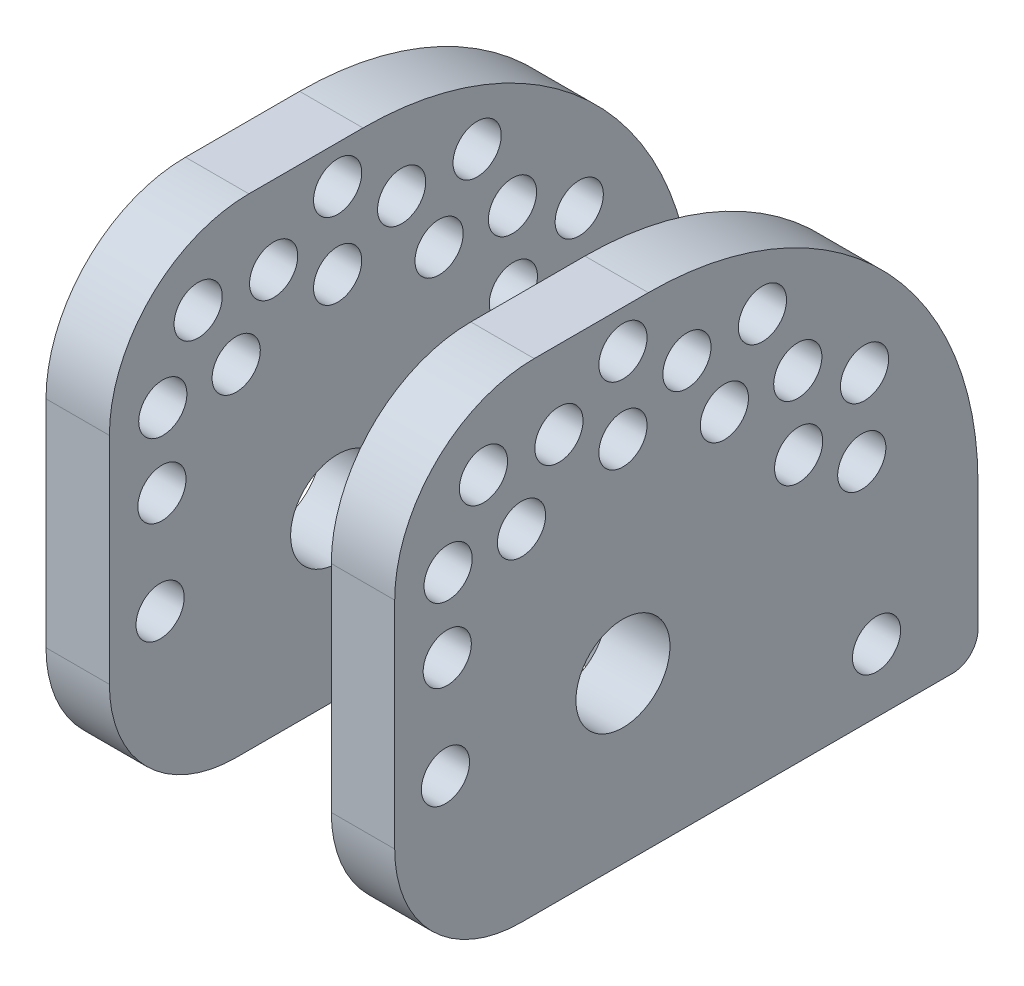
SolidWorks part; units mm, degrees
material "6061-T6 (SS)"
ref_plane "Front Plane" through (0, 0, 0) normal (0, 0, 1) x (1, 0, 0)
ref_plane "Top Plane" through (0, 0, 0) normal (0, 1, 0) x (1, 0, 0)
ref_plane "Right Plane" through (0, 0, 0) normal (1, 0, 0) x (0, 0, -1)
sketch "Top Outline" plane through (0, 0, 0) normal (0, 1, 0) x (1, 0, 0)
  line L0 (-133.35, -22.86) -> (133.35, -22.86) construction
  line L1 (-82.55, 0) -> (82.55, 0) construction
  line L2 (-58.42, 156.21) -> (-58.42, 0) construction
  line L3 (-58.42, 156.21) -> (58.42, 156.21) construction
  line L4 (58.42, 156.21) -> (58.42, 0) construction
  line L5 (0, 156.21) -> (0, 0) construction
  line L6 (-33.02, 156.21) -> (-33.02, 0) construction
  line L7 (33.02, 156.21) -> (33.02, 0) construction
  line L8 (-82.55, 56.515) -> (82.55, 56.515) construction
  line L9 (-58.42, 147.32) -> (58.42, 147.32) construction
  line L10 (0, 0) -> (0, -22.86) construction
  line L11 (-58.42, 73.66) -> (58.42, 73.66) construction
  line L12 (-133.35, -22.86) -> (-133.35, 156.21) construction
  line L13 (133.35, -22.86) -> (133.35, 156.21) construction
  circle A0 centre (-82.55, 0) radius 3.175 construction
  circle A1 centre (-82.55, 56.515) radius 3.175 construction
  circle A2 centre (82.55, 56.515) radius 3.175 construction
  circle A3 centre (82.55, 0) radius 3.175 construction
  point P7 (0, 56.515)
  point P8 (0, -22.86)
  point P21 (0, 0)
  dimension "D11" = 6.35
  dimension "D1" = 156.21
  dimension "D2" = 22.86
  dimension "D3" = 66.04
  dimension "D4" = 33.02
  dimension "D5" = 25.4
  dimension "D6" = 56.515
  dimension "D7" = 8.89
  dimension "D8" = 266.7
  dimension "D9" = 73.66
  dimension "D10" = 165.1
sketch "Side Outline" plane through (0, 0, 0) normal (1, 0, 0) x (0, 0, -1)
  line L0 (0, 0) -> (156.21, 0) construction
  line L1 (-22.86, 0) -> (156.21, 0) construction
  line L2 (0, 0) -> (0, 25.4) construction
  line L3 (156.21, 15.24) -> (0, 15.24) construction
  line L4 (0, 25.4) -> (156.21, 25.4) construction
  line L5 (156.21, 25.4) -> (156.21, 0) construction
  line L6 (-22.86, 74.6333) -> (-22.86, 0) construction
  line L7 (-22.86, 0) -> (0, 0) construction
  line L8 (-22.86, 74.6333) -> (147.32, 16.51) construction
  line L9 (73.66, 15.24) -> (73.66, 0) construction
  line L10 (56.515, 0) -> (56.515, 15.24) construction
  circle A0 centre (147.32, 16.51) radius 3.9624 construction
  circle A1 centre (-22.86, 16.51) radius 3.175 construction
  dimension "D5" = 7.9248
  dimension "D10" = 6.35
  dimension "D1" = 156.21
  dimension "D2" = 22.86
  dimension "D3" = 25.4
  dimension "D4" = 16.51
  dimension "D6" = 73.66
  dimension "D7" = 15.24
  dimension "D8" = 8.89
  dimension "D9" = 16.51
  dimension "D11" = 179.832
  dimension "D12" = 56.515
sketch "Sketch1" plane through (0, 0, 0) normal (1, 0, 0) x (0, 0, -1)
  line L0 (-12.7, 0) -> (-12.7, 15.24)
  line L1 (-22.86, 0) -> (156.21, 0) construction
  line L2 (-12.7, 15.24) -> (138.43, 15.24)
  line L3 (156.21, 15.24) -> (0, 15.24) construction
  line L4 (138.43, 15.24) -> (138.43, 16.51)
  line L5 (156.21, 0) -> (156.21, 16.51)
  line L6 (156.21, 25.4) -> (156.21, 0) construction
  line L8 (156.21, 0) -> (-12.7, 0)
  line L9 (0, 0) -> (0, 25.4) construction
  arc A0 (138.43, 16.51) -> (156.21, 16.51) centre (147.32, 16.51) cw
  dimension "D4" = 8.89
  dimension "D1" = 15.24
  dimension "D2" = 12.7
  dimension "D3" = 168.91
extrude "Center MC Body " add sketch "Sketch1" along normal blind 9.525
sketch "Sketch2" plane through (0, 0, 0) normal (1, 0, 0) x (0, 0, -1)
  line L0 (156.21, 25.4) -> (156.21, 0) construction
  line L1 (-22.86, 0) -> (156.21, 0) construction
  circle A0 centre (147.32, 16.51) radius 3.9624
  dimension "D3" = 7.9248
  dimension "D1" = 8.89
  dimension "D2" = 16.51
extrude "Center MC Hole" cut sketch "Sketch2" along normal blind 9.525
sketch "Sketch3" plane through (0, 0, 0) normal (1, 0, 0) x (0, 0, -1)
  line L0 (-6.35, 15.24) -> (12.7, 15.24)
  line L1 (156.21, 15.24) -> (0, 15.24) construction
  line L2 (12.7, 15.24) -> (12.7, 8.89)
  line L3 (12.7, 8.89) -> (-6.35, 8.89)
  line L5 (-6.35, 8.89) -> (-6.35, 15.24)
  line L6 (43.815, 15.24) -> (69.215, 15.24)
  line L7 (69.215, 15.24) -> (69.215, 8.89)
  line L8 (69.215, 8.89) -> (43.815, 8.89)
  line L9 (43.815, 8.89) -> (43.815, 15.24)
  line L12 (56.515, 8.89) -> (56.515, 0) construction
  line L13 (-22.86, 0) -> (156.21, 0) construction
  dimension "D1" = 19.05
  dimension "D2" = 25.4
  dimension "D3" = 8.89
  dimension "D4" = 56.515
  dimension "D5" = 12.7
extrude "Cut Slot" cut sketch "Sketch3" along normal blind 9.525
fillet "Fillet1" radius 12.7 1 edges at (4.7625, 0, -156.21)
fillet "Fillet2" radius 12.7 1 edges at (4.7625, 15.24, -138.43)
sketch "Sketch5" [suppressed] plane through (0, 0, 0) normal (1, 0, 0) x (0, 0, -1)
  line L0 (-12.7, 15.24) -> (43.815, 15.24)
  line L1 (43.815, 15.24) -> (43.815, 0) construction
  line L2 (156.21, 0) -> (0, 0) construction
  line L3 (43.815, 0) -> (-12.7, 0)
  line L4 (-12.7, 0) -> (-12.7, 15.24)
  arc A0 (43.815, 15.24) -> (43.815, 0) centre (43.815, 7.62) ccw
extrude "Cut-Extrude1" [suppressed] cut sketch "Sketch5" along normal through all
sketch "Sketch55" [suppressed] plane through (9.525, 0, 0) normal (1, 0, 0) x (0, 0, -1)
  line L6 (43.815, 0) -> (143.51, 0)
  line L7 (156.21, 12.7) -> (156.21, 16.51)
  line L8 (129.0038, 15.24) -> (69.215, 15.24)
  line L9 (69.215, 15.24) -> (69.215, 8.89)
  line L10 (69.215, 8.89) -> (43.815, 8.89)
  line L11 (43.815, 8.89) -> (43.815, 15.24)
  line L12 (43.815, 0) -> (143.51, 0)
  line L13 (156.21, 12.7) -> (156.21, 16.51)
  line L14 (129.0038, 15.24) -> (69.215, 15.24)
  line L15 (69.215, 15.24) -> (69.215, 8.89)
  line L16 (69.215, 8.89) -> (43.815, 8.89)
  line L17 (43.815, 8.89) -> (43.815, 15.24)
  circle A0 centre (147.32, 16.51) radius 3.9624 construction
  circle A1 centre (147.32, 16.51) radius 3.9624
  arc A4 (43.815, 15.24) -> (43.815, 0) centre (43.815, 7.62) ccw
  arc A5 (143.51, 0) -> (156.21, 12.7) centre (143.51, 12.7) ccw
  arc A6 (156.21, 16.51) -> (139.778, 21.2165) centre (147.32, 16.51) ccw
  arc A7 (129.0038, 15.24) -> (139.778, 21.2165) centre (129.0038, 27.94) ccw
  arc A8 (43.815, 15.24) -> (43.815, 0) centre (43.815, 7.62) ccw
  arc A9 (143.51, 0) -> (156.21, 12.7) centre (143.51, 12.7) ccw
  arc A10 (156.21, 16.51) -> (139.778, 21.2165) centre (147.32, 16.51) ccw
  arc A11 (129.0038, 15.24) -> (139.778, 21.2165) centre (129.0038, 27.94) ccw
  dimension "D1" = 0
extrude "Add Thickness 0.25" [suppressed] add sketch "Sketch55" along normal blind 6.35
sketch "Sketch56" [suppressed] plane through (0, 0, 0) normal (0, 1, 0) x (-1, 0, 0)
  line L0 (-7.9375, -129.54) -> (-7.9375, -78.74) construction
  line L1 (-12.7, -129.54) -> (-12.7, -78.74)
  line L2 (-3.175, -129.54) -> (-3.175, -78.74)
  line L3 (-7.9375, -129.0038) -> (-7.9375, -69.215) construction
  line L4 (-15.875, -129.0038) -> (0, -129.0038) construction
  line L5 (-15.875, -69.215) -> (0, -69.215) construction
  arc A0 (-12.7, -129.54) -> (-3.175, -129.54) centre (-7.9375, -129.54) ccw
  arc A1 (-3.175, -78.74) -> (-12.7, -78.74) centre (-7.9375, -78.74) ccw
  point P2 (-7.9375, -104.14)
  dimension "D1" = 9.525
  dimension "D2" = 9.525
  dimension "D3" = 50.8
extrude "Cut MC Slot" [suppressed] cut sketch "Sketch56" along normal through all
sketch "Sketch6" [suppressed] plane through (0, 0, 0) normal (0, 1, 0) x (1, 0, 0)
  line L0 (-88.9, 69.215) -> (88.9, 69.215)
  line L1 (88.9, 69.215) -> (88.9, 43.815)
  line L2 (88.9, 43.815) -> (-88.9, 43.815)
  line L3 (-88.9, 43.815) -> (-88.9, 69.215)
  line L4 (-82.55, 56.515) -> (82.55, 56.515) construction
  point P7 (0, 43.815)
  dimension "D1" = 25.4
  dimension "D2" = 12.7
  dimension "D3" = 177.8
extrude "Top Center Body" [suppressed] add sketch "Sketch6" along normal blind 15.875
sketch "Sketch7" [suppressed] plane through (0, 0, 0) normal (0, 1, 0) x (1, 0, 0)
  line L0 (-46.99, 69.215) -> (-46.99, 62.865)
  line L1 (88.9, 69.215) -> (-88.9, 69.215) construction
  line L2 (-46.99, 62.865) -> (-12.7, 62.865)
  line L3 (-12.7, 62.865) -> (-12.7, 69.215)
  line L4 (-12.7, 69.215) -> (-46.99, 69.215)
  line L5 (88.9, 43.815) -> (69.85, 43.815)
  line L6 (88.9, 50.165) -> (88.9, 43.815)
  line L7 (88.9, 50.165) -> (69.85, 50.165)
  line L8 (69.85, 50.165) -> (69.85, 43.815)
  line L9 (-88.9, 56.515) -> (88.9, 56.515) construction
  line L10 (46.99, 43.815) -> (46.99, 50.165)
  line L11 (-88.9, 69.215) -> (-88.9, 43.815) construction
  line L12 (88.9, 43.815) -> (88.9, 69.215) construction
  line L13 (0, 69.215) -> (0, 56.515) construction
  line L14 (0, 156.21) -> (0, 0) construction
  line L16 (12.7, 43.815) -> (46.99, 43.815)
  line L17 (12.7, 50.165) -> (12.7, 43.815)
  line L18 (46.99, 50.165) -> (12.7, 50.165)
  line L19 (46.99, 62.865) -> (12.7, 62.865)
  line L20 (-12.7, 50.165) -> (-12.7, 43.815)
  line L21 (-46.99, 50.165) -> (-12.7, 50.165)
  line L22 (-12.7, 43.815) -> (-46.99, 43.815)
  line L23 (-46.99, 43.815) -> (-46.99, 50.165)
  line L25 (-88.9, 62.865) -> (-69.85, 62.865)
  line L26 (-88.9, 62.865) -> (-88.9, 69.215)
  line L27 (-88.9, 69.215) -> (-69.85, 69.215)
  line L28 (-69.85, 62.865) -> (-69.85, 69.215)
  line L29 (12.7, 62.865) -> (12.7, 69.215)
  line L30 (12.7, 69.215) -> (46.99, 69.215)
  line L31 (46.99, 69.215) -> (46.99, 62.865)
  line L32 (88.9, 62.865) -> (69.85, 62.865)
  line L33 (69.85, 62.865) -> (69.85, 69.215)
  line L34 (88.9, 69.215) -> (69.85, 69.215)
  line L35 (88.9, 62.865) -> (88.9, 69.215)
  line L36 (-88.9, 50.165) -> (-69.85, 50.165)
  line L37 (-69.85, 50.165) -> (-69.85, 43.815)
  line L38 (-88.9, 43.815) -> (-69.85, 43.815)
  line L39 (-88.9, 50.165) -> (-88.9, 43.815)
  line L40 (-69.85, 69.215) -> (-46.99, 69.215) construction
  line L42 (88.9, 69.215) -> (-88.9, 69.215) construction
  point P20 (-58.42, 69.215)
  dimension "D1" = 19.05
  dimension "D2" = 58.42
  dimension "D3" = 6.35
  dimension "D4" = 12.7
extrude "Cut-Extrude31" [suppressed] cut sketch "Sketch7" along normal through all
sketch "Sketch9" [suppressed] plane through (0, 0, 0) normal (0, 1, 0) x (1, 0, 0)
  circle A0 centre (-82.55, 56.515) radius 3.175
  circle A1 centre (82.55, 56.515) radius 3.175
  dimension "D1" = 6.35
extrude "TC-Cut Holes" [suppressed] cut sketch "Sketch9" along normal through all
sketch "Sketch11" [suppressed] plane through (0, 0, -43.815) normal (0, 0, 1) x (1, 0, 0)
  line L0 (0, 0) -> (0, 8.89) construction
  line L2 (7.9375, 0) -> (-7.9375, 0)
  line L4 (-7.9375, 0) -> (-7.9375, 8.89)
  line L5 (-7.9375, 8.89) -> (7.9375, 8.89)
  line L7 (-63.1825, 0) -> (-53.6575, 0)
  line L8 (-63.1825, 0) -> (-63.1825, 8.89)
  line L9 (-63.1825, 8.89) -> (-53.6575, 8.89)
  line L10 (-53.6575, 0) -> (-53.6575, 8.89)
  line L11 (-58.42, 15.875) -> (-58.42, 0) construction
  line L13 (7.9375, 0) -> (7.9375, 8.89)
  line L14 (63.1825, 0) -> (63.1825, 8.89)
  line L15 (63.1825, 0) -> (53.6575, 0)
  line L16 (53.6575, 0) -> (53.6575, 8.89)
  line L17 (63.1825, 8.89) -> (53.6575, 8.89)
  line L18 (-20.6375, 8.89) -> (-20.6375, 0) construction
  line L19 (-25.4, 0) -> (-15.875, 0)
  line L20 (-25.4, 0) -> (-25.4, 8.89)
  line L21 (-25.4, 8.89) -> (-15.875, 8.89)
  line L22 (-15.875, 0) -> (-15.875, 8.89)
  line L23 (25.4, 0) -> (15.875, 0)
  line L24 (25.4, 0) -> (25.4, 8.89)
  line L25 (15.875, 0) -> (15.875, 8.89)
  line L26 (25.4, 8.89) -> (15.875, 8.89)
  line L28 (-69.85, 0) -> (-46.99, 0) construction
  line L29 (-12.7, 0) -> (12.7, 0) construction
  point P16 (-58.42, 0)
  point P23 (0, 8.89)
  dimension "D1" = 9.525
  dimension "D2" = 8.89
  dimension "D3" = 7.9375
  dimension "D4" = 58.42
  dimension "D5" = 15.875
  dimension "D6" = 9.525
extrude "TC-Cut Slots" [suppressed] cut sketch "Sketch11" against normal through all
fillet "Fillet8" [suppressed] radius 6.35
fillet "Fillet9" [suppressed] radius 3.175
sketch "Sketch12" plane through (0, 0, 0) normal (1, 0, 0) x (0, 0, -1)
  line L1 (56.515, 0) -> (156.21, 0)
  line L2 (56.515, 0) -> (56.515, 25.4)
  line L3 (56.515, 25.4) -> (156.21, 25.4)
  line L4 (156.21, 0) -> (156.21, 25.4)
extrude "Cut-Extrude2" cut sketch "Sketch12" along normal through all
sketch "Sketch13" plane through (0, 0, 0) normal (1, 0, 0) x (0, 0, -1)
  line L0 (43.815, 15.24) -> (50.165, 15.24)
  line L1 (50.165, 15.24) -> (50.165, 8.89)
  line L3 (50.165, 8.89) -> (62.865, 8.89)
  line L4 (62.865, 8.89) -> (62.865, 15.24)
  line L5 (62.865, 15.24) -> (66.675, 15.24)
  line L6 (66.675, 15.24) -> (66.675, 0)
  line L7 (156.21, 0) -> (0, 0) construction
  line L8 (66.675, 0) -> (43.815, 0)
  line L9 (43.815, 0) -> (43.815, 15.24)
  line L11 (56.515, 0) -> (56.515, 15.24) construction
  dimension "D1" = 6.35
  dimension "D2" = 12.7
  dimension "D3" = 3.81
extrude "Boss-Extrude1" add sketch "Sketch13" along normal up to surface (9.525 mm away) up to face at (9.525, 9.652, -18.796)
fillet "Fillet3" radius 3.175 2 edges at (4.7625, 0, -66.675) (4.7625, 15.24, -66.675)
sketch "Sketch14" plane through (0, 0, 0) normal (1, 0, 0) x (0, 0, -1)
  line L0 (-12.7, 0) -> (-35.56, 0)
  line L1 (-35.56, 0) -> (-35.56, 27.94)
  line L2 (-35.56, 27.94) -> (-12.7, 27.94)
  line L3 (-12.7, 27.94) -> (-12.7, 0)
  circle A0 centre (-22.86, 16.51) radius 4.7117
  dimension "D3" = 9.4234
  dimension "D1" = 27.94
  dimension "D2" = 22.86
extrude "Boss-Extrude2" add sketch "Sketch14" along normal blind 9.525
sketch "Sketch15" plane through (0, 0, 0) normal (1, 0, 0) x (0, 0, -1)
  line L0 (-12.7, 15.24) -> (-12.7, 27.94) construction
  line L1 (-6.35, 15.24) -> (-12.7, 15.24)
  line L2 (-6.35, 15.24) -> (-6.35, 8.89)
  line L3 (-6.35, 8.89) -> (-12.7, 8.89)
  line L4 (-12.7, 15.24) -> (-12.7, 8.89)
  line L5 (-6.35, 8.89) -> (12.7, 8.89) construction
extrude "Cut-Extrude3" [suppressed] cut sketch "Sketch15" along normal up to surface (9.525 mm away)
fillet "Fillet for Brake Pivot" [suppressed] radius 6.35
sketch "Sketch16" plane through (0, 0, 0) normal (1, 0, 0) x (0, 0, -1)
  line L1 (156.21, 0) -> (0, 0) construction
  line L2 (12.7, 0) -> (66.675, 0)
  line L3 (12.7, 0) -> (12.7, 15.24)
  line L4 (12.7, 15.24) -> (66.675, 15.24)
  line L5 (66.675, 0) -> (66.675, 15.24)
  line L7 (66.675, 3.175) -> (66.675, 12.065) construction
  dimension "D1" = 15.24
  dimension "D2" = 12.7
extrude "Cut for Throttle n Brake" cut sketch "Sketch16" along normal blind 9.525
sketch "Sketch17" plane through (0, 0, 0) normal (1, 0, 0) x (0, 0, -1)
  line L0 (0, 0) -> (-22.86, 0) construction
  line L1 (12.7, 0) -> (-45.72, 0)
  line L2 (12.7, 0) -> (12.7, 48.26)
  line L3 (12.7, 48.26) -> (-45.72, 48.26)
  line L4 (-45.72, 0) -> (-45.72, 48.26)
  line L6 (12.7, 8.89) -> (12.7, 0) construction
  circle A0 centre (-22.86, 16.51) radius 4.7117
  circle A1 centre (-22.86, 16.51) radius 4.7117 construction
  circle A2 centre (-22.86, 16.51) radius 12.7 construction
  arc A3 (8.635, 0) -> (-6.8459, 48.26) centre (-22.86, 16.51) ccw construction
  arc A4 (-38.8741, 48.26) -> (-45.72, 43.7485) centre (-22.86, 16.51) ccw construction
  dimension "D3" = 25.4
  dimension "D4" = 71.12
  dimension "D1" = 58.42
  dimension "D2" = 48.26
extrude "Boss-Extrude3" add sketch "Sketch17" along normal blind 9.525
sketch "Sketch44" plane through (9.525, 0, 0) normal (1, 0, 0) x (0, 0, -1)
  line L4 (12.7, 0) -> (12.7, 48.26)
  line L5 (12.7, 48.26) -> (-45.72, 48.26)
  line L6 (-45.72, 48.26) -> (-45.72, 0)
  line L7 (-45.72, 0) -> (12.7, 0)
  line L8 (12.7, 0) -> (12.7, 48.26)
  line L9 (12.7, 48.26) -> (-45.72, 48.26)
  line L10 (-45.72, 48.26) -> (-45.72, 0)
  line L11 (-45.72, 0) -> (12.7, 0)
  circle A0 centre (-22.86, 16.51) radius 4.7117 construction
  circle A1 centre (-22.86, 16.51) radius 4.7117
  dimension "D1" = 0
extrude "Boss-Extrude4" add sketch "Sketch44" along normal blind 25.4
sketch "Sketch20" plane through (0, 0, 0) normal (1, 0, 0) x (0, 0, -1)
  line L1 (-45.72, 16.51) -> (12.7, 16.51) construction
  line L2 (-45.72, 48.26) -> (-45.72, 0) construction
  line L3 (12.7, 48.26) -> (12.7, 0) construction
  circle A0 centre (-22.86, 16.51) radius 12.7 construction
  circle A3 centre (-22.86, 16.51) radius 17.78 construction
  circle A4 centre (-40.64, 16.51) radius 2.413
  dimension "D1" = 25.4
  dimension "D4" = 35.56
  dimension "D5" = 4.826
extrude "Cut-Extrude6" cut sketch "Sketch20" along normal through all
sketch "Sketch21" plane through (0, 0, 0) normal (1, 0, 0) x (0, 0, -1)
  line L0 (-43.18, 16.51) -> (-2.54, 16.51) construction
  line L1 (-40.4576, 26.67) -> (-22.86, 16.51) construction
  circle A0 centre (-22.86, 16.51) radius 20.32 construction
  circle A1 centre (-40.4576, 26.67) radius 2.413
  circle A2 centre (-40.64, 16.51) radius 2.413 construction
  dimension "D1" = 40.64
  dimension "D2" = 30
extrude "Cut-Extrude7" cut sketch "Sketch21" along normal through all
pattern_circular "CirPattern2" count 5 every 30 about axis through (0, 16.51, 22.86) along (1, 0, 0) of "Cut-Extrude7"
sketch "Sketch22" plane through (0, 0, 0) normal (1, 0, 0) x (0, 0, -1)
  line L0 (-47.625, 16.51) -> (1.905, 16.51) construction
  line L1 (-40.3715, 34.0215) -> (-22.86, 16.51) construction
  circle A0 centre (-22.86, 16.51) radius 24.765 construction
  circle A1 centre (-40.3715, 34.0215) radius 2.413
  circle A3 centre (-40.64, 16.51) radius 2.413 construction
  dimension "D1" = 49.53
  dimension "D2" = 45
extrude "Cut-Extrude10" cut sketch "Sketch22" along normal through all
pattern_circular "CirPattern3" count 5 every 30 about axis through (0, 16.51, 22.86) along (1, 0, 0) of "Cut-Extrude10"
sketch "Sketch24" plane through (0, 0, 0) normal (1, 0, 0) x (0, 0, -1)
  line L0 (-50.8, 16.51) -> (5.08, 16.51) construction
  line L1 (-36.83, 40.7067) -> (-22.86, 16.51) construction
  circle A0 centre (-22.86, 16.51) radius 27.94 construction
  circle A1 centre (-36.83, 40.7067) radius 2.413
  circle A2 centre (-40.64, 16.51) radius 2.413 construction
  dimension "D1" = 55.88
  dimension "D2" = 60
extrude "Cut-Extrude11" cut sketch "Sketch24" along normal through all
pattern_circular "CirPattern4" count 4 every 30 about axis through (0, 16.51, 22.86) along (1, 0, 0) of "Cut-Extrude11"
sketch "Sketch48" plane through (0, 0, 45.72) normal (0, 0, 1) x (1, 0, 0)
  line L0 (34.925, 0) -> (0, 0) construction
  line L1 (6.35, 0) -> (28.575, 0)
  line L2 (6.35, 0) -> (6.35, 107.2185)
  line L3 (6.35, 107.2185) -> (28.575, 107.2185)
  line L4 (28.575, 0) -> (28.575, 107.2185)
  line L5 (34.925, 48.26) -> (34.925, 0) construction
  point P6 (17.4625, 0)
  dimension "D1" = 6.35
extrude "Cut-Extrude24" cut sketch "Sketch48" against normal blind 38.1
sketch "Sketch49" plane through (0, 0, 7.62) normal (0, 0, 1) x (1, 0, 0)
  line L0 (6.35, 48.26) -> (28.575, 48.26) construction
  line L1 (6.35, 48.26) -> (28.575, 48.26)
  line L2 (6.35, 48.26) -> (6.35, 12.7)
  line L3 (6.35, 12.7) -> (28.575, 12.7)
  line L4 (28.575, 48.26) -> (28.575, 12.7)
  line L5 (6.35, 48.26) -> (6.35, 42.7585) construction
  line L6 (28.575, 0) -> (28.575, 26.1561) construction
  line L8 (6.35, 0) -> (28.575, 0) construction
  dimension "D1" = 12.7
extrude "Cut-Extrude25" cut sketch "Sketch49" against normal through all
fillet "Fillet4" radius 12.7 1 edges at (31.75, 0, 45.72)
fillet "Fillet5" radius 33.02 2 edges at (31.75, 48.26, -12.7) (3.175, 48.26, -12.7)
fillet "Fillet6" radius 13.97 1 edges at (31.75, 48.26, 45.72)
sketch "Sketch53" plane through (34.925, 0, 0) normal (1, 0, 0) x (0, 0, -1)
  line L0 (-33.02, 0) -> (12.7, 0) construction
  line L1 (12.7, 0) -> (12.7, 15.24) construction
  circle A0 centre (2.54, 6.35) radius 2.413
  dimension "D1" = 4.826
  dimension "D2" = 6.35
  dimension "D3" = 10.16
extrude "Cut-Extrude29" cut sketch "Sketch53" against normal through all
fillet "Fillet7" radius 2.54 1 edges at (17.4625, 0, -12.7)
sketch "Sketch26" [suppressed] plane through (0, 0, 0) normal (0, 1, 0) x (1, 0, 0)
  line L0 (-82.55, 0) -> (82.55, 0) construction
  line L1 (15.875, -12.7) -> (117.475, -12.7)
  line L2 (15.875, -12.7) -> (15.875, 12.7)
  line L3 (15.875, 12.7) -> (117.475, 12.7)
  line L4 (117.475, -12.7) -> (117.475, 12.7)
  line L5 (0, 12.7) -> (0, -12.7) construction
  point P10 (0, 0)
  dimension "D1" = 25.4
  dimension "D2" = 12.7
  dimension "D3" = 101.6
  dimension "D4" = 15.875
extrude "Top Right Body" [suppressed] add sketch "Sketch26" along normal blind 15.875 separate body
sketch "Sketch33" [suppressed] plane through (0, 0, 0) normal (0, 1, 0) x (1, 0, 0)
  circle A0 centre (82.55, 0) radius 3.175
  circle A1 centre (82.55, 0) radius 3.175 construction
extrude "Cut-Extrude14" [suppressed] cut sketch "Sketch33" along normal through all
sketch "Sketch34" [suppressed] plane through (0, 0, 12.7) normal (0, 0, 1) x (1, 0, 0)
  line L0 (15.875, 15.875) -> (15.875, 0) construction
  line L1 (15.875, 8.89) -> (25.4, 8.89)
  line L2 (15.875, 8.89) -> (15.875, 0)
  line L3 (15.875, 0) -> (25.4, 0)
  line L4 (25.4, 8.89) -> (25.4, 0)
  line L5 (15.875, 0) -> (117.475, 0) construction
  line L6 (15.875, 15.875) -> (117.475, 15.875) construction
  line L7 (53.6575, 0) -> (63.1825, 0)
  line L8 (53.6575, 0) -> (53.6575, 8.89)
  line L9 (53.6575, 8.89) -> (63.1825, 8.89)
  line L10 (63.1825, 0) -> (63.1825, 8.89)
  line L15 (58.42, 15.875) -> (58.42, 0) construction
  line L16 (0, 15.875) -> (0, 0) construction
  point P18 (58.42, 0)
  dimension "D1" = 9.525
  dimension "D2" = 8.89
  dimension "D3" = 58.42
extrude "Cut-Extrude15" [suppressed] cut sketch "Sketch34" against normal through all
sketch "Sketch35" [suppressed] plane through (0, 15.875, 0) normal (0, 1, 0) x (1, 0, 0)
  line L0 (15.875, -12.7) -> (117.475, -12.7) construction
  line L1 (53.6575, -12.7) -> (63.1825, -12.7)
  line L2 (53.6575, -12.7) -> (53.6575, -6.35)
  line L3 (53.6575, -6.35) -> (63.1825, -6.35)
  line L4 (63.1825, -12.7) -> (63.1825, -6.35)
  line L12 (58.42, 12.7) -> (58.42, -12.7) construction
  line L13 (117.475, 12.7) -> (15.875, 12.7) construction
  line L14 (58.42, 156.21) -> (58.42, 0) construction
  point P14 (58.42, -6.35)
  dimension "D1" = 6.35
  dimension "D2" = 9.525
extrude "Cut-Extrude16" [suppressed] cut sketch "Sketch35" against normal through all
sketch "Sketch36" [suppressed] plane through (0, 0, 12.7) normal (0, 0, 1) x (1, 0, 0)
  line L0 (0, 0) -> (0, 15.875) construction
  line L1 (0, 7.9375) -> (92.075, 7.9375) construction
  line L3 (15.875, 15.875) -> (15.875, 8.89) construction
  line L4 (53.6575, 15.875) -> (53.6575, 0) construction
  circle A0 centre (46.355, 7.9375) radius 3.175
  circle A1 centre (92.075, 7.9375) radius 3.175
  point P13 (53.6575, 7.9375)
  dimension "D1" = 6.35
  dimension "D2" = 30.48
  dimension "D3" = 76.2
extrude "Cut-Extrude17" [suppressed] cut sketch "Sketch36" against normal through all
sketch "Sketch52" [suppressed] plane through (117.475, 0, 0) normal (1, 0, 0) x (0, 0, -1)
  line L0 (12.7, 15.875) -> (12.7, 0) construction
  line L1 (-12.7, 0) -> (12.7, 0) construction
  circle A0 centre (2.54, 6.35) radius 2.413
  dimension "D3" = 4.826
  dimension "D1" = 10.16
  dimension "D2" = 6.35
extrude "Cut-Extrude28" [suppressed] cut sketch "Sketch52" against normal blind 15.24
sketch "Sketch37" [suppressed] plane through (0, 0, 0) normal (0, 1, 0) x (1, 0, 0)
  line L0 (0, 0) -> (0, -22.86) construction
  line L1 (-15.875, -12.7) -> (-117.475, -12.7)
  line L2 (-15.875, -12.7) -> (-15.875, 12.7)
  line L3 (-15.875, 12.7) -> (-117.475, 12.7)
  line L4 (-117.475, -12.7) -> (-117.475, 12.7)
  line L5 (-82.55, 0) -> (82.55, 0) construction
  dimension "D1" = 15.875
  dimension "D2" = 101.6
  dimension "D3" = 12.7
  dimension "D4" = 25.4
extrude "Top Left Body" [suppressed] add sketch "Sketch37" along normal blind 15.875
sketch "Sketch38" [suppressed] plane through (0, 0, 0) normal (0, 1, 0) x (1, 0, 0)
  circle A0 centre (-82.55, 0) radius 3.175
  circle A1 centre (-82.55, 0) radius 3.175 construction
extrude "Cut-Extrude18" [suppressed] cut sketch "Sketch38" along normal through all
sketch "Sketch40" [suppressed] plane through (0, 0, 12.7) normal (0, 0, 1) x (1, 0, 0)
  line L0 (-117.475, 0) -> (-15.875, 0) construction
  line L1 (-15.875, 0) -> (-25.4, 0)
  line L2 (-15.875, 0) -> (-15.875, 8.89)
  line L3 (-15.875, 8.89) -> (-25.4, 8.89)
  line L4 (-25.4, 0) -> (-25.4, 8.89)
  line L5 (-63.1825, 0) -> (-53.6575, 0)
  line L6 (-63.1825, 0) -> (-63.1825, 8.89)
  line L7 (-63.1825, 8.89) -> (-53.6575, 8.89)
  line L8 (-53.6575, 0) -> (-53.6575, 8.89)
  line L9 (-117.475, 15.875) -> (-15.875, 15.875) construction
  line L14 (-58.42, 15.875) -> (-58.42, 0) construction
  line L15 (0, 15.875) -> (0, 0) construction
  line L16 (-15.875, 15.875) -> (-15.875, 0) construction
  point P24 (-58.42, 8.89)
  dimension "D1" = 8.89
  dimension "D2" = 9.525
  dimension "D3" = 58.42
extrude "Cut-Extrude19" [suppressed] cut sketch "Sketch40" against normal through all
sketch "Sketch41" [suppressed] plane through (0, 15.875, 0) normal (0, 1, 0) x (1, 0, 0)
  line L0 (-117.475, -12.7) -> (-15.875, -12.7) construction
  line L1 (-63.1825, -12.7) -> (-53.6575, -12.7)
  line L2 (-63.1825, -12.7) -> (-63.1825, -6.35)
  line L3 (-63.1825, -6.35) -> (-53.6575, -6.35)
  line L4 (-53.6575, -12.7) -> (-53.6575, -6.35)
  line L6 (0, -12.7) -> (0, 0) construction
  line L11 (-53.6575, -12.7) -> (-63.1825, -12.7) construction
  line L12 (-58.42, -6.35) -> (-58.42, -12.7) construction
  dimension "D1" = 6.35
  dimension "D2" = 58.42
extrude "Cut-Extrude20" [suppressed] cut sketch "Sketch41" against normal through all
sketch "Sketch42" [suppressed] plane through (0, 0, 12.7) normal (0, 0, 1) x (1, 0, 0)
  line L2 (-117.475, 0) -> (-63.1825, 0) construction
  line L3 (-15.875, 15.875) -> (-15.875, 8.89) construction
  circle A0 centre (-46.355, 7.9375) radius 3.175
  circle A1 centre (-92.075, 7.9375) radius 3.175
  dimension "D1" = 6.35
  dimension "D2" = 30.48
  dimension "D3" = 76.2
  dimension "D4" = 7.9375
extrude "Cut-Extrude21" [suppressed] cut sketch "Sketch42" against normal through all
sketch "Sketch54" [suppressed] plane through (-117.475, 0, 0) normal (-1, 0, 0) x (0, 0, 1)
  line L0 (-12.7, 0) -> (12.7, 0) construction
  line L1 (-12.7, 15.875) -> (-12.7, 0) construction
  circle A0 centre (-2.54, 6.35) radius 2.413
  dimension "D3" = 4.826
  dimension "D1" = 6.35
  dimension "D2" = 10.16
extrude "Cut-Extrude30" [suppressed] cut sketch "Sketch54" against normal blind 15.24
